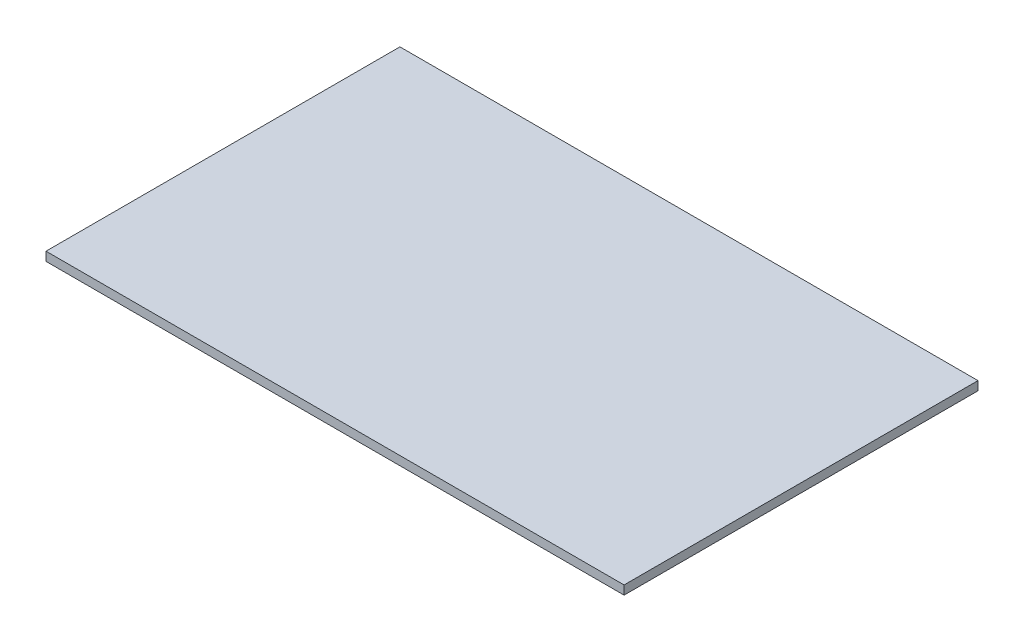
SolidWorks part; units mm, degrees
ref_plane "Спереди" through (0, 0, 0) normal (0, 0, 1) x (1, 0, 0)
ref_plane "Сверху" through (0, 0, 0) normal (0, 1, 0) x (1, 0, 0)
ref_plane "Справа" through (0, 0, 0) normal (1, 0, 0) x (0, 0, -1)
sketch "Эскиз1" plane through (0, 0, 0) normal (0, 1, 0) x (1, 0, 0)
  line L1 (-49, 30) -> (49, 30)
  line L2 (-49, 30) -> (-49, -30)
  line L3 (-49, -30) -> (49, -30)
  line L4 (49, 30) -> (49, -30)
  line L5 (-49, 30) -> (49, -30) construction
  line L6 (-49, -30) -> (49, 30) construction
  point P0 (0, 0)
extrude "Бобышка-Вытянуть1" add sketch "Эскиз1" along normal blind 1.5
